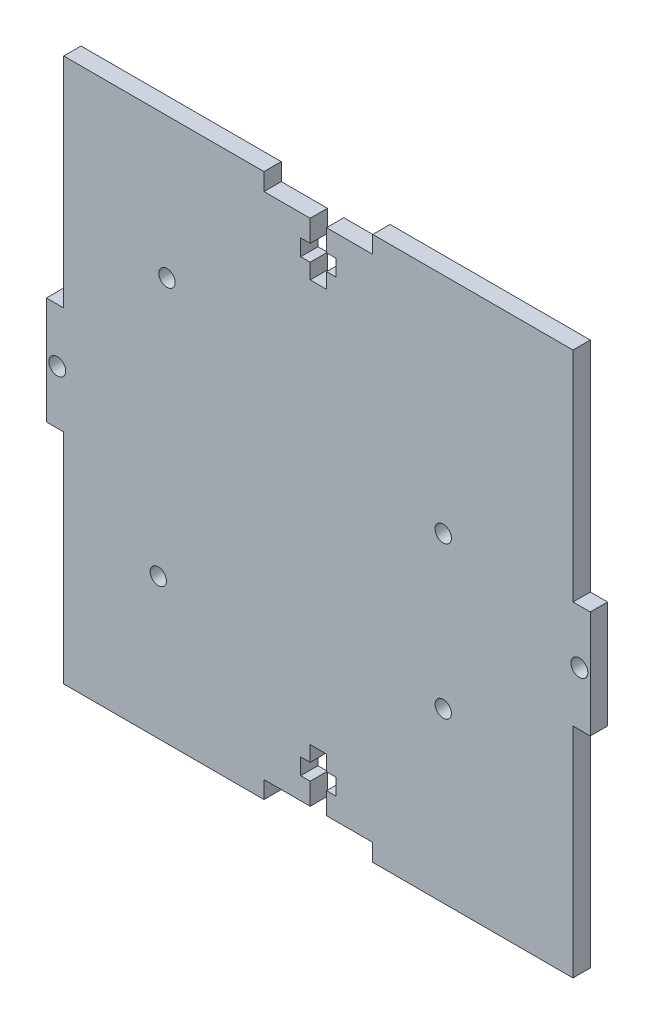
SolidWorks part; units mm, degrees
ref_plane "Front Plane" through (0, 0, 0) normal (0, 0, 1) x (1, 0, 0)
ref_plane "Top Plane" through (0, 0, 0) normal (0, 1, 0) x (1, 0, 0)
ref_plane "Right Plane" through (0, 0, 0) normal (1, 0, 0) x (0, 0, -1)
sketch "Sketch1" plane through (0, 0, 0) normal (0, 0, 1) x (1, 0, 0)
  line L0 (0, 40) -> (0, -40) construction
  line L5 (-50, -50) -> (50, 50) construction
  line L6 (-50, 50) -> (50, -50) construction
  line L7 (-100, 0) -> (100, 0) construction
  line L32 (-50, 50) -> (50, 50)
  line L35 (50, 50) -> (50, -50)
  line L36 (50, -50) -> (-50, -50)
  line L37 (-50, -50) -> (-50, 50)
  point P0 (0, 0)
  dimension "D1" = 100
  dimension "D2" = 100
extrude "Boss-Extrude2" add sketch "Sketch1" along normal blind 3.18
sketch "Sketch2" plane through (0, 0, 3.18) normal (0, 0, 1) x (1, 0, 0)
  line L0 (0, -50) -> (0, 50) construction
  line L1 (-123.0225, 0) -> (147.0753, 0) construction
  line L2 (50, 50) -> (-50, 50) construction
  line L4 (-10, 50) -> (-10, 46.82)
  line L5 (-10, 46.82) -> (-1.5, 46.82)
  line L6 (10, 50) -> (10, 46.82)
  line L7 (1.5, 46.82) -> (10, 46.82)
  line L9 (-1.5, 46.82) -> (-1.5, 42.82)
  line L10 (-1.5, 37) -> (1.5, 37)
  line L11 (1.5, 46.82) -> (1.5, 42.82)
  line L12 (-3.25, 42.82) -> (-1.5, 42.82)
  line L13 (-3.25, 42.82) -> (-3.25, 39.82)
  line L14 (-3.25, 39.82) -> (-1.5, 39.82)
  line L15 (3.25, 42.82) -> (3.25, 39.82)
  line L16 (1.5, 42.82) -> (3.25, 42.82)
  line L17 (-1.5, 39.82) -> (-1.5, 37)
  line L18 (1.5, 39.82) -> (1.5, 37)
  line L19 (1.5, 39.82) -> (3.25, 39.82)
  line L20 (-10, 50) -> (10, 50)
  line L21 (-50, -50) -> (50, -50) construction
  line L22 (-50, 50) -> (-50, -50) construction
  line L23 (-50, 9.875) -> (-46.82, 9.875)
  line L24 (-50, 9.875) -> (-50, 50)
  line L25 (-50, 50) -> (-46.82, 50)
  line L26 (-46.82, 9.875) -> (-46.82, 50)
  line L28 (-50, -9.875) -> (-46.82, -9.875)
  line L29 (-50, -9.875) -> (-50, -50)
  line L30 (-50, -50) -> (-46.82, -50)
  line L31 (-46.82, -9.875) -> (-46.82, -50)
  circle A0 centre (-48, 0) radius 1.55
  dimension "D11" = 3.1
  dimension "D12" = 2
  dimension "D1" = 4
  dimension "D2" = 3
  dimension "D3" = 3
  dimension "D4" = 20
  dimension "D5" = 6.5
  dimension "D6" = 3.18
  dimension "D7" = 13
  dimension "D8" = 19.75
  dimension "D9" = 3.18
  dimension "D10" = 3.18
extrude "Cut-Extrude1" cut sketch "Sketch2" against normal through all
mirror "Mirror1" about plane through (0, 0, 0) normal (0, 1, 0) of "Cut-Extrude1"
mirror "Mirror3" about plane through (0, 0, 0) normal (1, 0, 0) of "Cut-Extrude1"
sketch "Sketch3" plane through (0, 0, 0) normal (0, 0, -1) x (-1, 0, 0)
  circle A0 centre (27.8324, 24.15) radius 1.5
  circle A1 centre (29.4324, -24.15) radius 1.5
  circle A2 centre (-22.9676, -19.05) radius 1.5
  circle A3 centre (-22.9676, 8.85) radius 1.5
  dimension "D1" = 3
  dimension "D2" = 3
  dimension "D3" = 3
  dimension "D4" = 3
extrude "Cut-Extrude2" cut sketch "Sketch3" against normal through all
